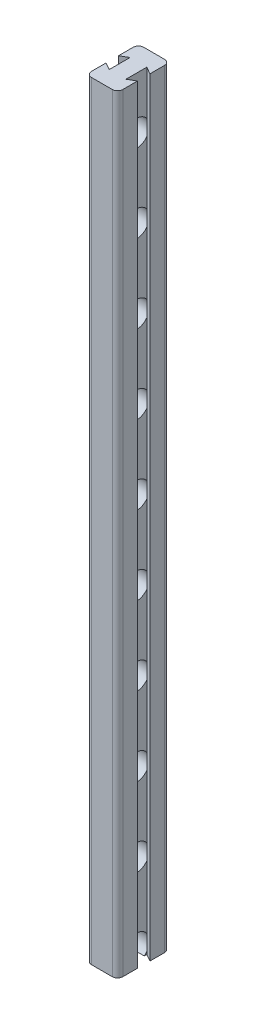
SolidWorks part; units mm, degrees
material "5052-H32"
ref_plane "Front Plane" through (0, 0, 0) normal (0, 0, 1) x (1, 0, 0)
ref_plane "Top Plane" through (0, 0, 0) normal (0, 1, 0) x (1, 0, 0)
ref_plane "Right Plane" through (0, 0, 0) normal (1, 0, 0) x (0, 0, -1)
sketch "Sketch1" plane through (0, 0, 0) normal (0, 1, 0) x (1, 0, 0)
  line L5 (15, 25) -> (15, 5.9585)
  line L6 (15, 5.9585) -> (8, 10)
  line L7 (8, 10) -> (8, -10)
  line L8 (8, -10) -> (15, -5.9585)
  line L9 (15, -5.9585) -> (15, -25)
  line L16 (-15, -25) -> (-15, -5.9585)
  line L17 (-15, -5.9585) -> (-8, -10)
  line L18 (-8, -10) -> (-8, 10)
  line L19 (-8, 10) -> (-15, 5.9585)
  line L20 (-15, 5.9585) -> (-15, 25)
  line L21 (0, 34.0363) -> (0, -31.0073) construction
  line L22 (-32.2836, 0) -> (31.3226, 0) construction
  line L23 (-15, 25) -> (15, 25)
  line L24 (-15, -25) -> (15, -25)
  point P2 (0, 25)
  point P30 (-8, 0)
  point P43 (8, 0)
  dimension "D5" = 7
  dimension "D6" = 7
  dimension "D7" = 20
  dimension "D8" = 60
  dimension "D10" = 60
  dimension "D11" = 30
  dimension "D12" = 60
  dimension "D13" = 60
extrude "Boss-Extrude1" add sketch "Sketch1" along normal blind 735
sketch "Sketch3" plane through (0, 0, 0) normal (1, 0, 0) x (0, 0, -1)
  line L0 (-10, 735) -> (10, 735) construction
  line L2 (25, 735) -> (25, 0) construction
  circle A0 centre (0, 685) radius 12.5
  circle A1 centre (0, 610) radius 12.5
  circle A2 centre (0, 535) radius 12.5
  circle A3 centre (0, 460) radius 12.5
  circle A4 centre (0, 385) radius 12.5
  circle A5 centre (0, 310) radius 12.5
  circle A6 centre (0, 235) radius 12.5
  circle A7 centre (0, 160) radius 12.5
  circle A8 centre (0, 85) radius 12.5
  circle A9 centre (0, 10) radius 12.5
  circle A10 centre (0, -65) radius 12.5
  dimension "D1" = 25
  dimension "D2" = 50
  dimension "D3" = 25
  dimension "D4" = 11
extrude "Cut-Extrude2" cut sketch "Sketch3" against normal blind 8 and the other way blind 8
fillet "Fillet1" radius 5 4 edges at (15, 367.5, 25) (15, 367.5, -25) (-15, 367.5, -25) (-15, 367.5, 25)
